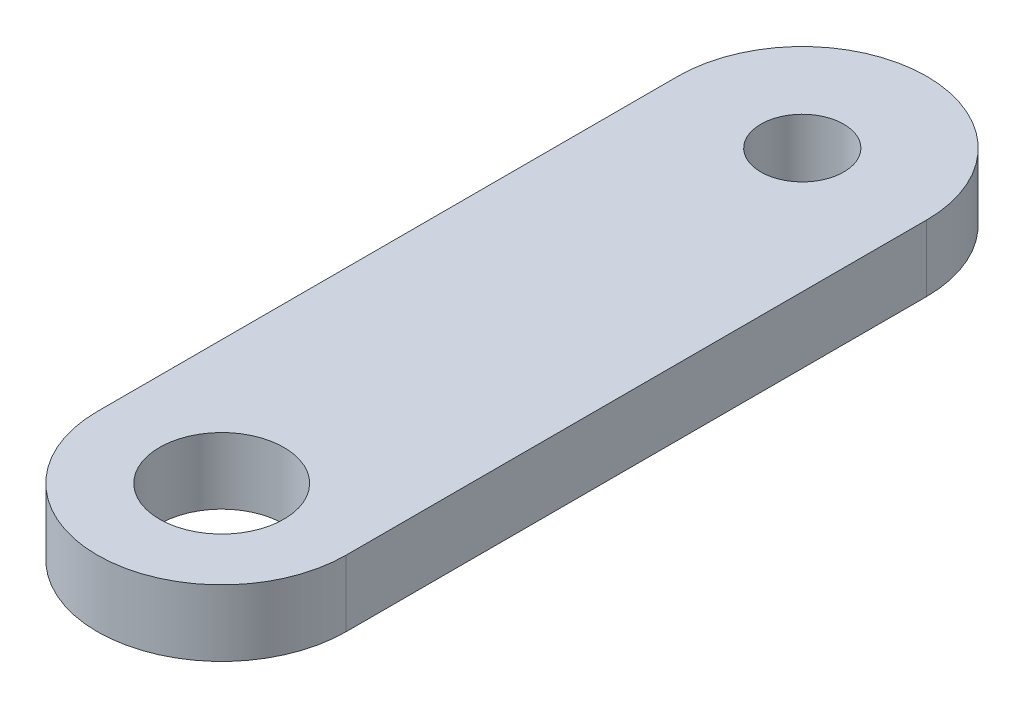
SolidWorks part; units mm, degrees
material "ABS"
ref_plane "Front Plane" through (0, 0, 0) normal (0, 0, 1) x (1, 0, 0)
ref_plane "Top Plane" through (0, 0, 0) normal (0, 1, 0) x (1, 0, 0)
ref_plane "Right Plane" through (0, 0, 0) normal (1, 0, 0) x (0, 0, -1)
sketch "Sketch1" plane through (0, 0, 0) normal (0, 1, 0) x (1, 0, 0)
  line L0 (0, 22.225) -> (0, 0) construction
  line L1 (4.7625, 22.225) -> (4.7625, 0)
  line L2 (-4.7625, 22.225) -> (-4.7625, 0)
  circle A0 centre (0, 0) radius 2.3813
  circle A1 centre (0, 22.225) radius 1.5875
  arc A2 (4.7625, 22.225) -> (-4.7625, 22.225) centre (0, 22.225) ccw
  arc A3 (-4.7625, 0) -> (4.7625, 0) centre (0, 0) ccw
  point P5 (0, 11.1125)
  dimension "D1" = 4.7625
  dimension "D2" = 3.175
  dimension "D3" = 22.225
  dimension "D4" = 9.525
extrude "Boss-Extrude1" add sketch "Sketch1" along normal blind 2.54
